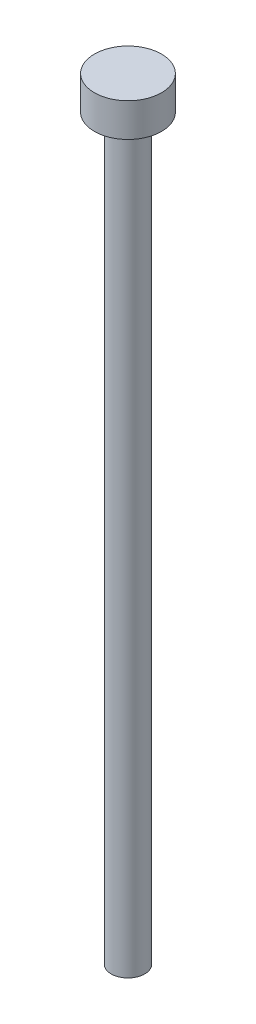
SolidWorks part; units mm, degrees
ref_plane "Front Plane" through (0, 0, 0) normal (0, 0, 1) x (1, 0, 0)
ref_plane "Top Plane" through (0, 0, 0) normal (0, 1, 0) x (1, 0, 0)
ref_plane "Right Plane" through (0, 0, 0) normal (1, 0, 0) x (0, 0, -1)
sketch "Sketch1" plane through (0, 0, 0) normal (0, 1, 0) x (1, 0, 0)
  circle A0 centre (0, 0) radius 1.5
extrude "Boss-Extrude1" add sketch "Sketch1" along normal blind 66
sketch "Sketch2" plane through (0, 66, 0) normal (0, 1, 0) x (1, 0, 0)
  circle A0 centre (0, 0) radius 3
extrude "Boss-Extrude2" add sketch "Sketch2" along normal blind 3
fillet "Fillet1" radius 1 1 edges at (0, 66, 1.5)
